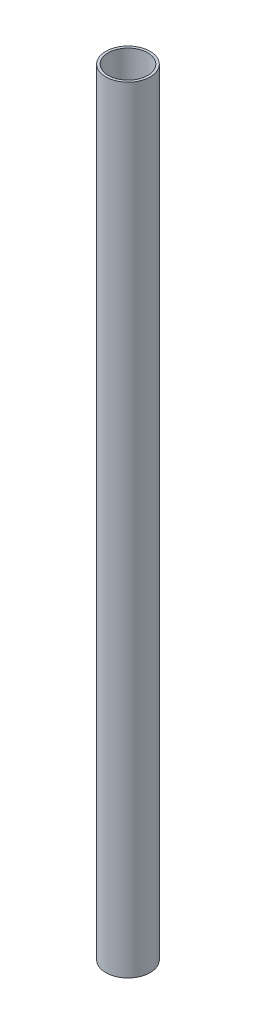
SolidWorks part; units mm, degrees
ref_plane "Alzado" through (0, 0, 0) normal (0, 0, 1) x (1, 0, 0)
ref_plane "Planta" through (0, 0, 0) normal (0, 1, 0) x (1, 0, 0)
ref_plane "Vista lateral" through (0, 0, 0) normal (1, 0, 0) x (0, 0, -1)
sketch "Croquis1" plane through (0, 0, 0) normal (0, 1, 0) x (1, 0, 0)
  circle A0 centre (0, 0) radius 8
  circle A1 centre (0, 0) radius 9
  dimension "D1" = 1
  dimension "D2" = 16
extrude "Saliente-Extruir1" add sketch "Croquis1" along normal blind 315
